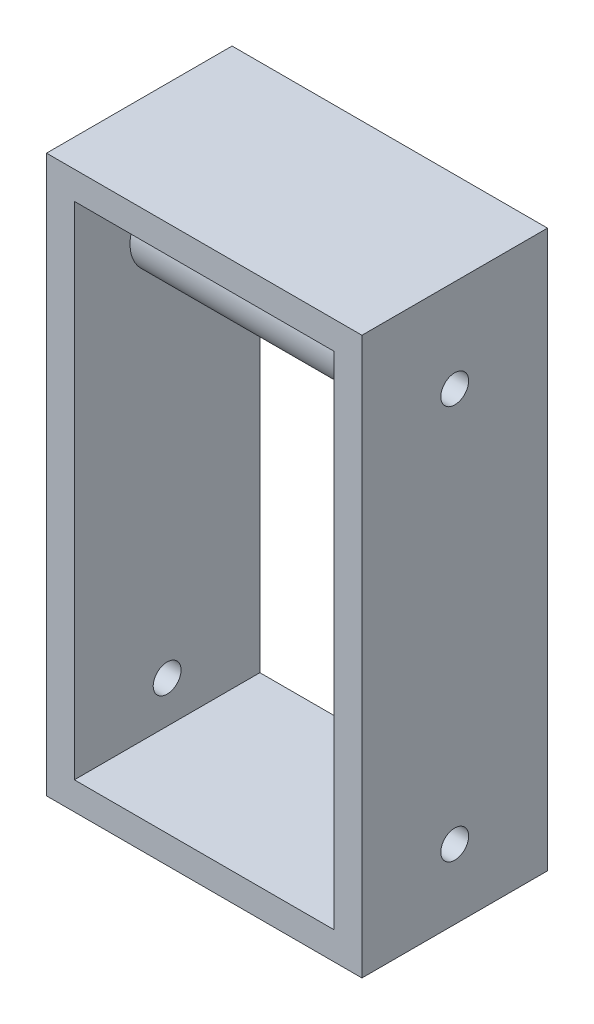
SolidWorks part; units mm, degrees
ref_plane "Front Plane" through (0, 0, 0) normal (0, 0, 1) x (1, 0, 0)
ref_plane "Top Plane" through (0, 0, 0) normal (0, 1, 0) x (1, 0, 0)
ref_plane "Right Plane" through (0, 0, 0) normal (1, 0, 0) x (0, 0, -1)
sketch "Sketch1" plane through (0, 0, 0) normal (0, 0, 1) x (1, 0, 0)
  line L0 (-14, 27) -> (-14, -27)
  line L1 (-17, 30) -> (17, 30)
  line L2 (-17, 30) -> (-17, -30)
  line L3 (-17, -30) -> (17, -30)
  line L4 (17, 30) -> (17, -30)
  line L5 (-17, 30) -> (17, -30) construction
  line L6 (-17, -30) -> (17, 30) construction
  line L7 (-14, -27) -> (14, -27)
  line L8 (14, 27) -> (14, -27)
  line L9 (-14, 27) -> (14, 27)
  point P0 (0, 0)
  dimension "D1" = 34
  dimension "D2" = 60
  dimension "D3" = 3
extrude "Boss-Extrude1" add sketch "Sketch1" along normal blind 20
sketch "Sketch2" plane through (17, 0, 0) normal (1, 0, 0) x (0, 0, -1)
  line L0 (-10, 30) -> (-10, -30) construction
  line L1 (-20, 30) -> (0, 30) construction
  line L2 (-20, -30) -> (0, -30) construction
  line L3 (-20, 30) -> (0, 30) construction
  circle A0 centre (-10, -22.5) radius 1.5
  circle A1 centre (-10, 20) radius 1.5
  dimension "D1" = 3
  dimension "D2" = 7.5
  dimension "D3" = 3
  dimension "D4" = 10
extrude "Cut-Extrude1" cut sketch "Sketch2" against normal through all both and the other way through all
sketch "Sketch4" plane through (14, 0, 0) normal (-1, 0, 0) x (0, 0, 1)
  circle A0 centre (10, 20) radius 4
  dimension "D1" = 8
extrude "Boss-Extrude2" add sketch "Sketch4" along normal up to surface (28 mm away) up to face at (-14, -21, 10)
